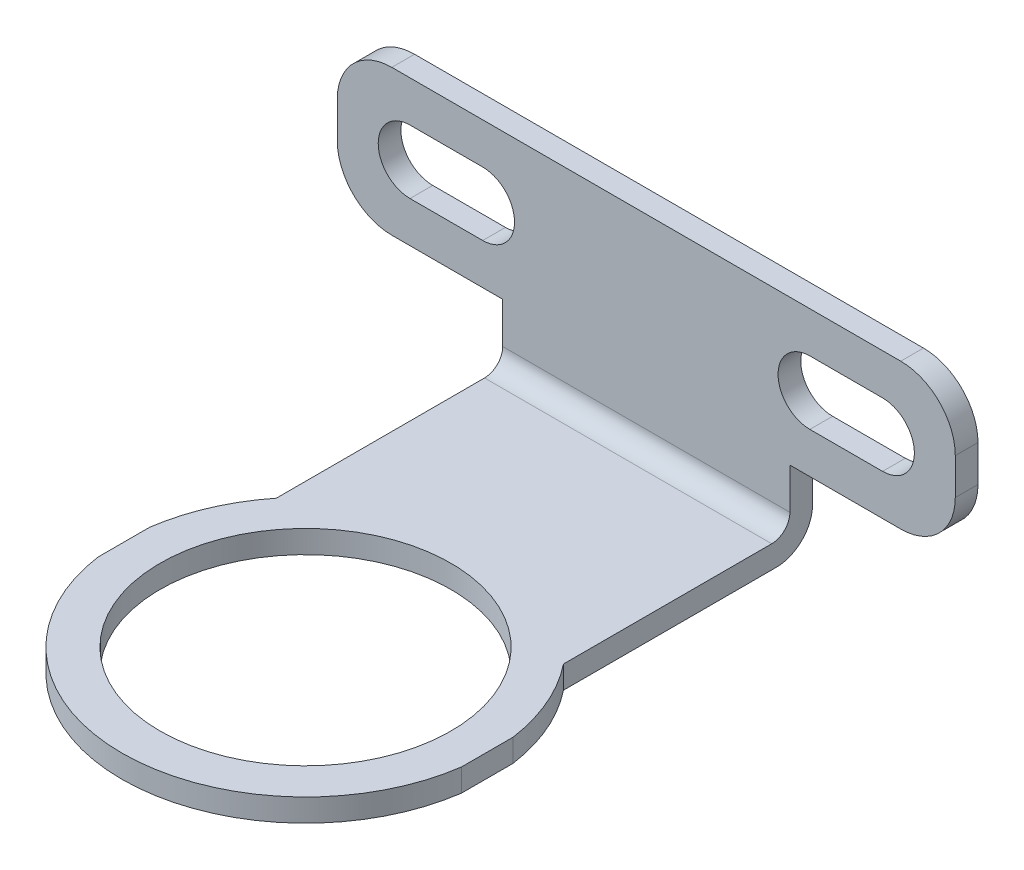
SolidWorks part; units mm, degrees
ref_plane "Front Plane" through (0, 0, 0) normal (0, 0, 1) x (1, 0, 0)
ref_plane "Top Plane" through (0, 0, 0) normal (0, 1, 0) x (1, 0, 0)
ref_plane "Right Plane" through (0, 0, 0) normal (1, 0, 0) x (0, 0, -1)
ref_plane "Plane1" through (0, 2.5, 0) normal (0, 1, 0) x (1, 0, 0)
sketch "Sketch1" plane through (0, 2.5, 0) normal (0, 1, 0) x (1, 0, 0)
  line L0 (20, -42.8355) -> (20, 0)
  line L1 (20, 0) -> (-20, 0)
  line L2 (-20, 0) -> (-20, -42.8355)
  arc A0 (-20, -42.8355) -> (20, -42.8355) centre (0, -40) ccw
extrude "Boss-Extrude1" add sketch "Sketch1" against normal blind 2.5
sketch "Sketch2" plane through (0, 0, 0) normal (0, -1, 0) x (1, 0, 0)
  line L0 (-15.8, 0) -> (-15.8, 27.4143)
  line L1 (-20, 37.1645) -> (-20, 0)
  line L2 (-20, 0) -> (-15.8, 0)
  arc A0 (-15.8, 27.4143) -> (-20, 37.1645) centre (0, 40) cw
extrude "Cut-Extrude1" cut sketch "Sketch2" against normal through all
sketch "Sketch3" plane through (0, 0, 0) normal (0, -1, 0) x (1, 0, 0)
  line L0 (20, 0) -> (20, 37.1645)
  line L1 (15.8, 27.4143) -> (15.8, 0)
  line L2 (15.8, 0) -> (20, 0)
  arc A0 (20, 37.1645) -> (15.8, 27.4143) centre (0, 40) cw
extrude "Cut-Extrude2" cut sketch "Sketch3" against normal through all
sketch "Sketch4" plane through (0, 2.5, 0) normal (0, 1, 0) x (-1, 0, 0)
  line L0 (-15.8, 2.5) -> (15.8, 2.5)
  line L1 (15.8, 2.5) -> (15.8, 0)
  line L2 (15.8, 0) -> (-15.8, 0)
  line L3 (-15.8, 0) -> (-15.8, 2.5)
extrude "Boss-Extrude2" add sketch "Sketch4" along normal blind 22.5
sketch "Sketch5" plane through (15.8, 0, 0) normal (1, 0, 0) x (0, 0, -1)
  line L0 (0, 25) -> (0, 9)
  line L1 (0, 9) -> (-2.5, 9)
  line L2 (-2.5, 9) -> (-2.5, 25)
  line L3 (-2.5, 25) -> (0, 25)
extrude "Boss-Extrude3" add sketch "Sketch5" along normal blind 18.2
sketch "Sketch6" plane through (-15.8, 0, 0) normal (-1, 0, 0) x (0, 0, 1)
  line L0 (0, 9) -> (0, 25)
  line L1 (0, 25) -> (2.5, 25)
  line L2 (2.5, 25) -> (2.5, 9)
  line L3 (2.5, 9) -> (0, 9)
extrude "Boss-Extrude4" add sketch "Sketch6" along normal blind 18.2
sketch "Sketch7" plane through (0, 0, 2.5) normal (0, 0, 1) x (1, 0, 0)
  line L0 (26, 20.5) -> (18, 20.5)
  line L1 (18, 13.5) -> (26, 13.5)
  arc A0 (26, 13.5) -> (26, 20.5) centre (26, 17) ccw
  arc A1 (18, 20.5) -> (18, 13.5) centre (18, 17) ccw
extrude "Cut-Extrude3" cut sketch "Sketch7" against normal through all
sketch "Sketch8" plane through (0, 0, 0) normal (0, 0, -1) x (-1, 0, 0)
  line L0 (26, 20.5) -> (18, 20.5)
  line L1 (18, 13.5) -> (26, 13.5)
  arc A0 (18, 20.5) -> (18, 13.5) centre (18, 17) ccw
  arc A1 (26, 13.5) -> (26, 20.5) centre (26, 17) ccw
extrude "Cut-Extrude4" cut sketch "Sketch8" against normal through all
hole_wizard "M27 Clearance Hole1" positions "Sketch10" profile "Sketch9" hole size "M27" standard "ANSI Metric"
sketch "Sketch10" plane through (0, 2.5, 0) normal (0, 1, 0) x (1, 0, 0)
  point P0 (0, -40)
sketch "Sketch9" plane through (0, 2.5, 40) normal (1, 0, 0) x (0, 0, 1)
  line L0 (0, 0) -> (0, 2.5)
  line L1 (0, 2.5) -> (16, 2.5)
  line L2 (16, 2.5) -> (16, 0)
  line L5 (16, 0) -> (0, 0)
  line L11 (0, -6.35) -> (0, 107.95) construction
  dimension "Thru Hole Dia." = 32
  dimension "Thru Hole Depth" = 2.5
fillet "Fillet1" radius 2 1 edges at (0, 2.5, 2.5)
fillet "Fillet2" radius 4 1 edges at (0, 0, 0)
fillet "Fillet3" radius 6 4 edges at (-34, 25, 1.25) (-34, 9, 1.25) (34, 9, 1.25) (34, 25, 1.25)
